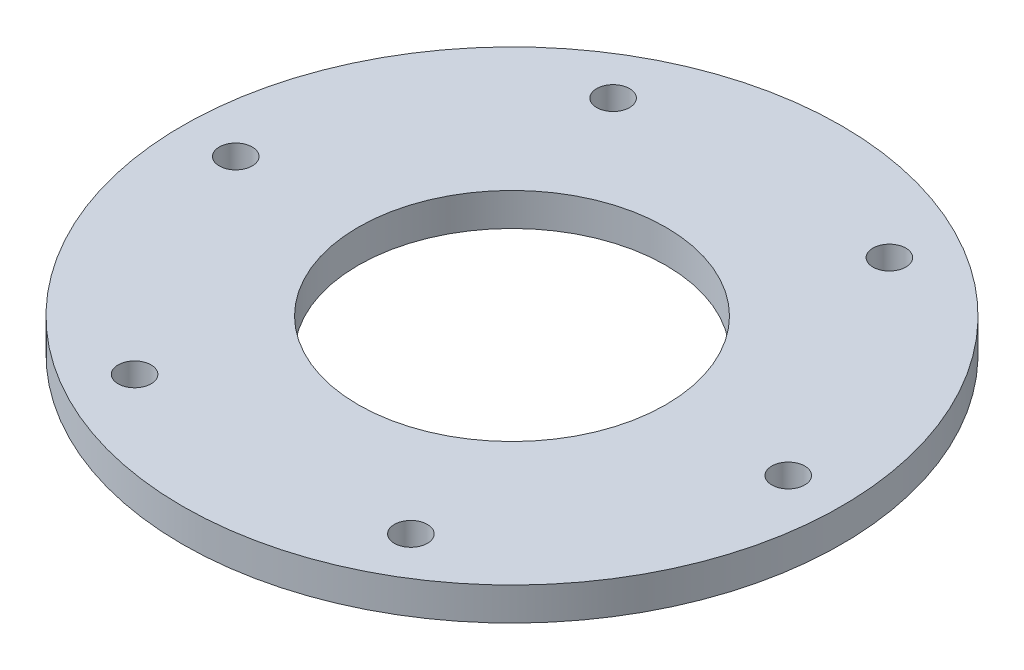
SolidWorks part; units mm, degrees
ref_plane "Front Plane" through (0, 0, 0) normal (0, 0, 1) x (1, 0, 0)
ref_plane "Top Plane" through (0, 0, 0) normal (0, 1, 0) x (1, 0, 0)
ref_plane "Right Plane" through (0, 0, 0) normal (1, 0, 0) x (0, 0, -1)
sketch "Sketch1" plane through (0, 0, 0) normal (0, 1, 0) x (1, 0, 0)
  line L0 (0, 0) -> (-25.15, 0) construction
  circle A0 centre (0, 0) radius 25.15 construction
  circle A1 centre (-25.15, 0) radius 1.5
  circle A2 centre (0, 0) radius 14
  circle A3 centre (0, 0) radius 30
  circle A4 centre (-12.575, 21.7805) radius 1.5
  circle A5 centre (12.575, 21.7805) radius 1.5
  circle A6 centre (25.15, 0) radius 1.5
  circle A7 centre (12.575, -21.7805) radius 1.5
  circle A8 centre (-12.575, -21.7805) radius 1.5
  point P19 (0, 0)
  dimension "D1" = 50.3
  dimension "D2" = 3
  dimension "D3" = 28
  dimension "D4" = 60
  dimension "D6" = 25.15
  dimension "D5" = 6
extrude "Boss-Extrude1" add sketch "Sketch1" along normal blind 3
